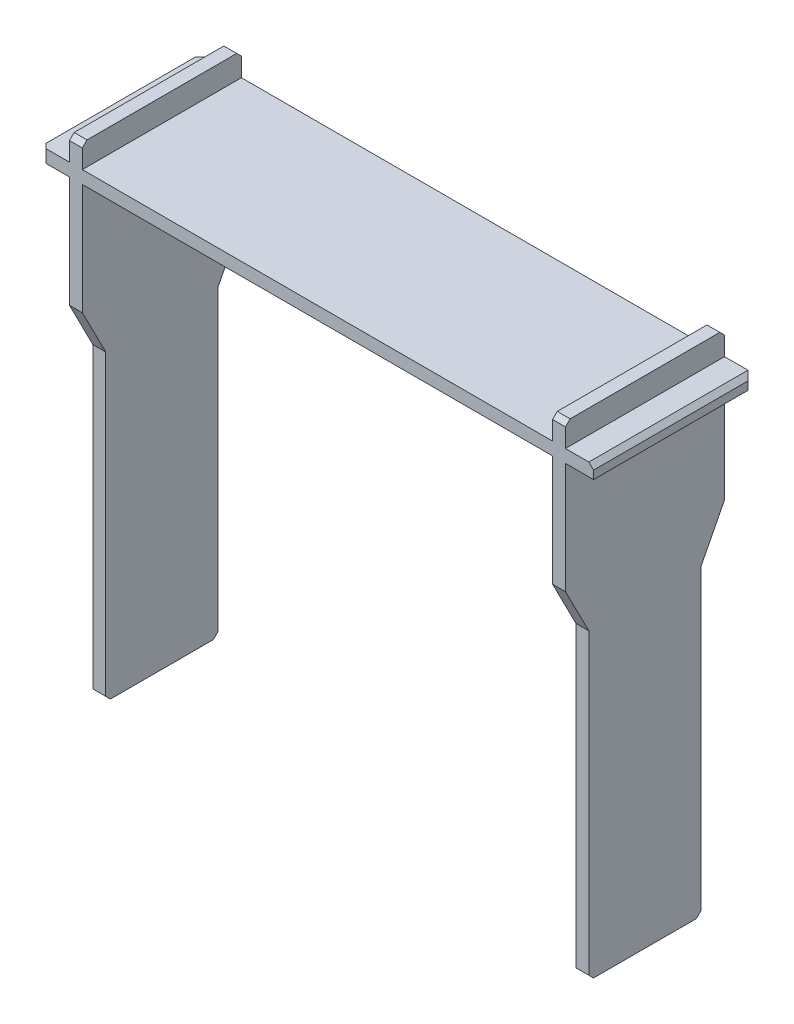
SolidWorks part; units mm, degrees
ref_plane "Front Plane" through (0, 0, 0) normal (0, 0, 1) x (1, 0, 0)
ref_plane "Top Plane" through (0, 0, 0) normal (0, 1, 0) x (1, 0, 0)
ref_plane "Right Plane" through (0, 0, 0) normal (1, 0, 0) x (0, 0, -1)
sketch "Sketch1" plane through (0, 0, 0) normal (0, 0, 1) x (1, 0, 0)
  line L0 (0, -55) -> (0, 55) construction
  line L1 (-59, -1.375) -> (59, -1.375)
  line L2 (-59, -1.375) -> (-59, 1.375)
  line L3 (-59, 1.375) -> (59, 1.375)
  line L4 (59, -1.375) -> (59, 1.375)
  line L5 (-59, -1.375) -> (59, 1.375) construction
  line L6 (-59, 1.375) -> (59, -1.375) construction
  line L7 (-53, -99.625) -> (-50.25, -99.625)
  line L8 (-53, -99.625) -> (-53, 6.375)
  line L9 (-53, 6.375) -> (-50.25, 6.375)
  line L10 (-50.25, -99.625) -> (-50.25, 6.375)
  line L11 (-53, -99.625) -> (-50.25, 6.375) construction
  line L12 (-53, 6.375) -> (-50.25, -99.625) construction
  line L13 (53, 6.375) -> (50.25, 6.375)
  line L14 (50.25, -99.625) -> (50.25, 6.375)
  line L15 (53, -99.625) -> (50.25, -99.625)
  line L16 (53, -99.625) -> (53, 6.375)
  point P0 (0, 0)
  point P6 (-51.625, -46.625)
  dimension "D1" = 118
  dimension "D2" = 2.75
  dimension "D3" = 106
  dimension "D4" = 5
  dimension "D5" = 6
  dimension "D6" = 2.75
extrude "Boss-Extrude1" add sketch "Sketch1" along normal mid plane 34 contours L3 L10 L9 L8 | L1 L8 L3 L2 | L1 L10 L3 L8 | L7 L10 L1 L8 | L1 L14 L3 L10 | L3 L16 L13 L14 | L1 L16 L3 L14 | L16 L1 L4 L3 | L15 L16 L1 L14
sketch "Sketch2" plane through (53, 0, 0) normal (1, 0, 0) x (0, 0, -1)
  line L0 (-17, -25.125) -> (-12, -34.875)
  line L1 (-17, -99.625) -> (-17, -1.375) construction
  line L2 (-12, -34.875) -> (-12, -99.625)
  line L3 (-17, -99.625) -> (17, -99.625) construction
  line L4 (-12, -99.625) -> (12, -99.625)
  line L5 (12, -99.625) -> (12, -34.875)
  line L6 (12, -34.875) -> (17, -25.125)
  line L7 (17, -99.625) -> (17, -1.375) construction
  line L8 (17, -25.125) -> (17, -99.625)
  line L9 (17, -99.625) -> (12, -99.625)
  line L10 (-12, -99.625) -> (-17, -99.625)
  line L11 (-17, -99.625) -> (-17, -25.125)
  line L12 (-12, -34.875) -> (12, -34.875) construction
  line L13 (-17, -25.125) -> (17, -25.125)
  point P4 (16.3003, -38.0056)
  point P17 (6.2, -50.0874)
  line M9 (17, -99.625) -> (17, -1.375)
  line M11 (-17, -1.375) -> (-17, -99.625)
  line M12 (-17, -99.625) -> (17, -99.625)
  dimension "D1" = 64.75
  dimension "D2" = 74.5
  dimension "D3" = 24
extrude "Cut-Extrude1" cut sketch "Sketch2" against normal through all contours L2 L0 M11 M12 | L6 L5 M12 M9
chamfer "Chamfer1" distance 1 angle 45 12 edges at (-59, 0, -17) (-59, 0, 17) (-51.625, 6.375, -17) (-51.625, 6.375, 17) (51.625, 6.375, -17) (51.625, 6.375, 17) (59, 1.375, 0) (59, 0, -17) (51.625, -99.625, -12) (51.625, -99.625, 12) (-51.625, -99.625, 12) (-51.625, -99.625, -12)
